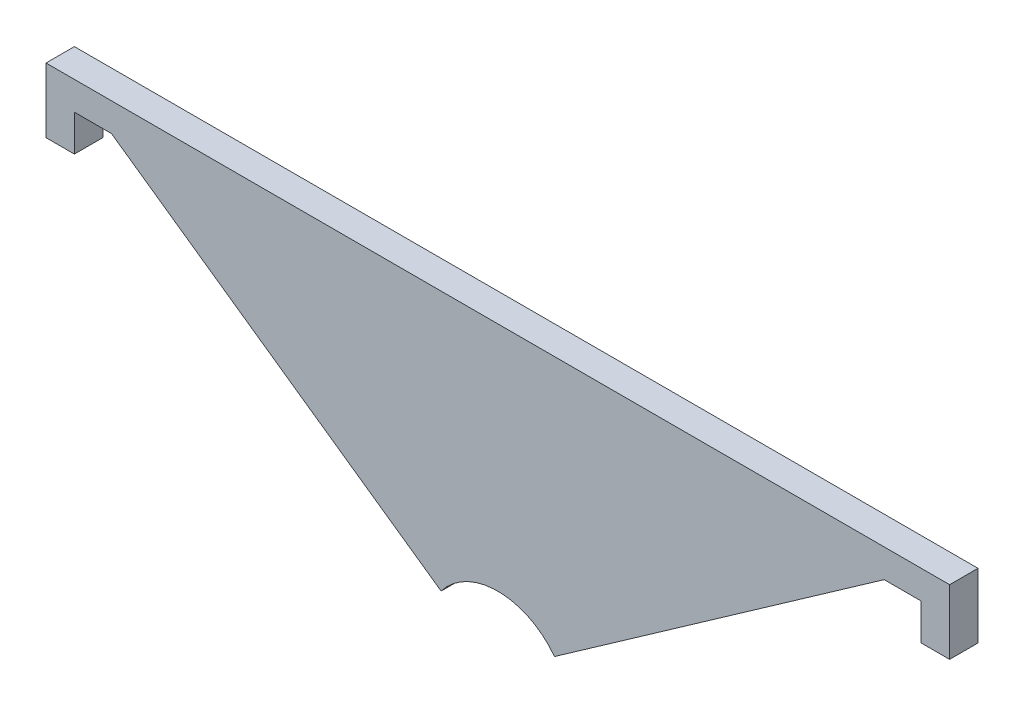
SolidWorks part; units mm, degrees
ref_plane "Plan de face" through (0, 0, 0) normal (0, 0, 1) x (1, 0, 0)
ref_plane "Plan de dessus" through (0, 0, 0) normal (0, 1, 0) x (1, 0, 0)
ref_plane "Plan de droite" through (0, 0, 0) normal (1, 0, 0) x (0, 0, -1)
sketch "Esquisse1" plane through (0, 0, 0) normal (0, 0, 1) x (1, 0, 0)
  line L0 (0, 0) -> (0, 20.2323) construction
  line L2 (-56.5, 0) -> (-56.5, 5) construction
  line L3 (-56.5, 5) -> (-44.5, 5) construction
  line L4 (-44.5, 13.3425) -> (-44.5, 72.3618) construction
  line L11 (-56.5, 0) -> (-35.792, 0) construction
  line L28 (-13.1159, 49.7073) -> (-44.5, 5) construction
  line L29 (-35.792, 0) -> (-21.7522, 20) construction
  line L30 (35.792, 0) -> (21.7522, 20) construction
  line L31 (13.1159, 49.7073) -> (44.5, 5) construction
  line L32 (56.5, 0) -> (35.792, 0) construction
  line L33 (56.5, 5) -> (44.5, 5) construction
  line L34 (56.5, 0) -> (56.5, 5) construction
  line L35 (-21.7522, 20) -> (21.7522, 20) construction
  line L36 (44.5, 5) -> (15.9887, 45.6149) construction
  line L37 (0, 40.5) -> (13.1159, 49.7073) construction
  line L49 (-44.5, 65.6296) -> (-44.5, 69.2189) construction
  line L50 (-44.5, 69.2189) -> (-40.9107, 69.2189) construction
  line L51 (-40.9107, 69.2189) -> (-13.1159, 49.7073) construction
  line L52 (-15.9887, 45.6149) -> (-44.5, 65.6296) construction
  line L54 (-44.5, 5) -> (-15.9887, 45.6149) construction
  line L55 (-13.1159, 49.7073) -> (-6.1385, 44.8092) construction
  line L56 (6.1385, 44.8092) -> (13.1159, 49.7073) construction
  line L57 (44.5, 65.6296) -> (44.5, 69.2189) construction
  line L58 (44.5, 69.2189) -> (40.9107, 69.2189) construction
  line L59 (15.9887, 45.6149) -> (44.5, 65.6296) construction
  line L60 (40.9107, 69.2189) -> (13.1159, 49.7073) construction
  line L61 (-17.0873, 35.3475) -> (-25.8445, 22.8728) construction
  line L62 (-25.8445, 22.8728) -> (-3.3233, 22.8728) construction
  line L63 (-21.7522, 20) -> (-29.9368, 25.7456) construction
  line L64 (-3.3233, 22.8728) -> (-3.3233, 25.8728) construction
  line L65 (-17.0873, 35.3475) -> (-14.0873, 35.3475) construction
  line L66 (0, 40.5) -> (0, 56.525) construction
  line L67 (17.0873, 35.3475) -> (14.0873, 35.3475) construction
  line L68 (3.3233, 22.8728) -> (3.3233, 25.8728) construction
  line L69 (25.8445, 22.8728) -> (3.3233, 22.8728) construction
  line L70 (17.0873, 35.3475) -> (25.8445, 22.8728) construction
  circle A1 centre (0, 40.5) radius 11.025 construction
  arc A3 (13.1159, 49.7073) -> (-13.1159, 49.7073) centre (0, 40.5) ccw construction
  circle A5 centre (0, 40.5) radius 7 construction
  arc A6 (-6.1385, 44.8092) -> (6.1385, 44.8092) centre (0, 40.5) ccw construction
  arc A7 (-3.3233, 25.8728) -> (-14.0873, 35.3475) centre (0, 40.5) cw construction
  arc A8 (3.3233, 25.8728) -> (14.0873, 35.3475) centre (0, 40.5) ccw construction
  point P17 (0, 20)
  dimension "D1" = 22.05
  dimension "D5" = 5
  dimension "D9" = 14
  dimension "D10" = 0.5
  dimension "D12" = 15
  dimension "D2" = 40.5
  dimension "D3" = 5
  dimension "D4" = 12
  dimension "D6" = 10
  dimension "D7" = 56.5
  dimension "D8" = 20
  dimension "D11" = 5
  dimension "D13" = 3
sketch "Esquisse2" plane through (0, 0, 0) normal (0, 0, 1) x (1, 0, 0)
  line L0 (-47.75, 65.6296) -> (-44.75, 65.6296)
  line L1 (0, 40.5) -> (0, 56.525) construction
  line L2 (-44.75, 65.6296) -> (-44.75, 69.4689)
  line L3 (-44.75, 69.4689) -> (-40.8317, 69.4689)
  line L4 (-40.8317, 69.4689) -> (-5.9914, 45.0114)
  line L5 (-40.9107, 69.2189) -> (-13.1159, 49.7073) construction
  line L6 (-44.5, 69.2189) -> (-40.9107, 69.2189) construction
  line L7 (-44.5, -199986.6575) -> (-44.5, 200072.3618) construction
  line L8 (-47.75, 65.6296) -> (-47.75, 72.4689)
  line L9 (47.75, 72.4689) -> (-47.75, 72.4689)
  line L10 (0, -200000) -> (0, 200020.2323) construction
  line L11 (47.75, 65.6296) -> (47.75, 72.4689)
  line L12 (40.8317, 69.4689) -> (5.9914, 45.0114)
  line L13 (44.75, 69.4689) -> (40.8317, 69.4689)
  line L14 (44.75, 65.6296) -> (44.75, 69.4689)
  line L15 (47.75, 65.6296) -> (44.75, 65.6296)
  arc A0 (5.9914, 45.0114) -> (-5.9914, 45.0114) centre (0, 40.5) ccw
  arc A1 (-6.1385, 44.8092) -> (6.1385, 44.8092) centre (0, 40.5) ccw construction
  point P18 (0, 72.4689)
  dimension "D1" = 0.25
  dimension "D2" = 0.25
  dimension "D3" = 0.25
  dimension "D4" = 3
  dimension "D5" = 3
extrude "Boss.-Extru.1" add sketch "Esquisse2" along normal blind 3
